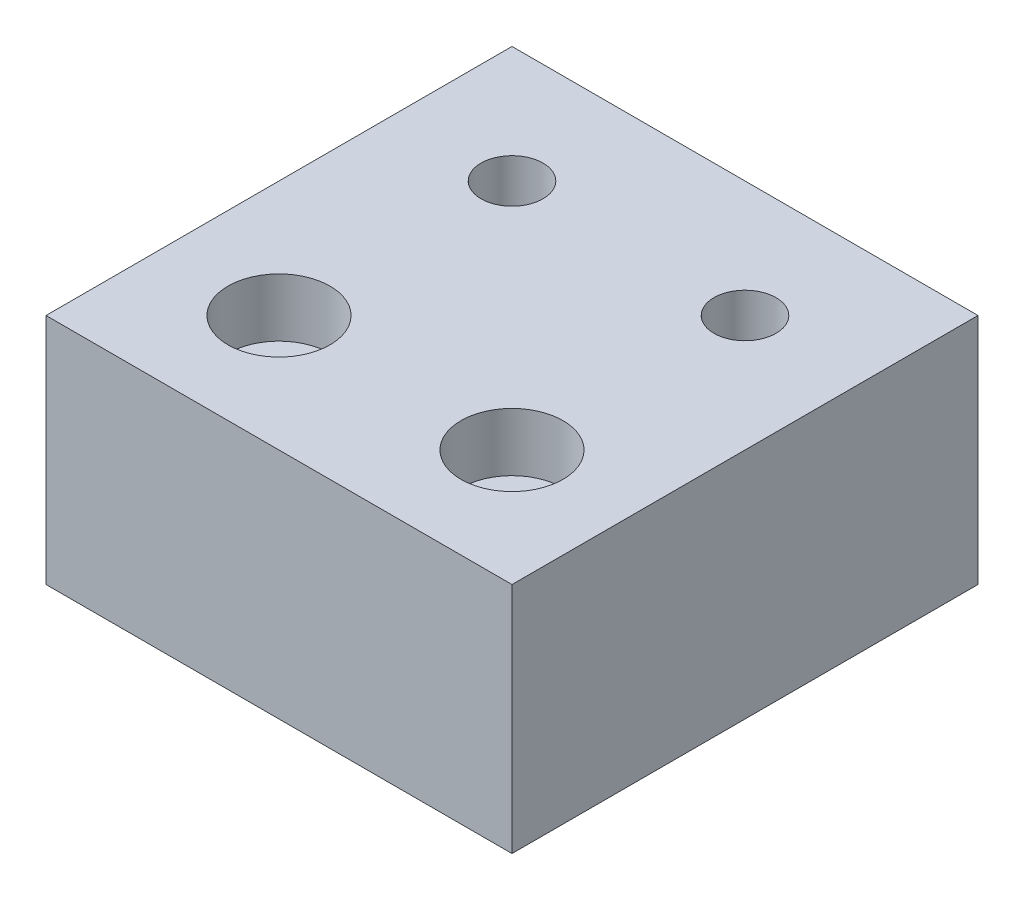
SolidWorks part; units mm, degrees
ref_plane "Front Plane" through (0, 0, 0) normal (0, 0, 1) x (1, 0, 0)
ref_plane "Top Plane" through (0, 0, 0) normal (0, 1, 0) x (1, 0, 0)
ref_plane "Right Plane" through (0, 0, 0) normal (1, 0, 0) x (0, 0, -1)
sketch "Sketch1" plane through (0, 0, 0) normal (0, 1, 0) x (1, 0, 0)
  line L1 (0, 0) -> (101.6, 0)
  line L2 (0, 0) -> (0, 50.8)
  line L3 (0, 50.8) -> (101.6, 50.8)
  line L4 (101.6, 0) -> (101.6, 50.8)
extrude "Boss-Extrude1" add sketch "Sketch1" along normal blind 25.4
hole_wizard "CBORE for 1/4 Socket Head Cap Screw1" positions "Sketch4" profile "Sketch3" counterbore size "1/4" standard "Ansi Inch" end condition through all
sketch "Sketch4" plane through (0, 25.4, 0) normal (0, 1, 0) x (-1, 0, 0)
  point P0 (-12.7, -12.7)
sketch "Sketch3" plane through (12.7, 25.4, -12.7) normal (1, 0, 0) x (0, 0, 1)
  line L0 (0, 0) -> (0, 25.4)
  line L1 (0, 25.4) -> (3.3782, 25.4)
  line L3 (3.3782, 25.4) -> (3.3782, 6.35)
  line L4 (3.3782, 6.35) -> (5.5562, 6.35)
  line L5 (5.5562, 6.35) -> (5.5563, 0)
  line L7 (5.5563, 0) -> (0, 0)
  line L11 (0, -6.35) -> (0, 107.95) construction
  dimension "Thru Hole Dia." = 6.7564
  dimension "Thru Hole Depth" = 25.4
  dimension "C'Bore Dia." = 11.1125
  dimension "C'Bore Depth" = 6.35
pattern_linear "LPattern1" count 1 spacing 25.4 along (0, 0, 1) count 4 spacing 25.4 along (1, 0, 0) of "CBORE for 1/4 Socket Head Cap Screw1"
hole_wizard "1/4 Clearance Hole1" positions "Sketch6" profile "Sketch5" hole size "1/4" standard "Ansi Inch" end condition through all
sketch "Sketch6" plane through (0, 25.4, 0) normal (0, 1, 0) x (-1, 0, 0)
  point P0 (-12.7, -38.1)
sketch "Sketch5" plane through (12.7, 25.4, -38.1) normal (1, 0, 0) x (0, 0, 1)
  line L0 (0, 0) -> (0, 25.4)
  line L1 (0, 25.4) -> (3.3782, 25.4)
  line L2 (3.3782, 25.4) -> (3.3782, 0)
  line L5 (3.3782, 0) -> (0, 0)
  line L11 (0, -6.35) -> (0, 107.95) construction
  dimension "Thru Hole Dia." = 6.7564
  dimension "Thru Hole Depth" = 25.4
pattern_linear "LPattern2" count 4 spacing 25.4 along (1, 0, 0) of "1/4 Clearance Hole1"
sketch "Sketch7" plane through (101.6, 0, 0) normal (1, 0, 0) x (0, 0, -1)
  line L1 (0, 0) -> (50.8, 0)
  line L2 (0, 0) -> (0, 25.4)
  line L3 (0, 25.4) -> (50.8, 25.4)
  line L4 (50.8, 0) -> (50.8, 25.4)
extrude "Cut-Extrude1" cut sketch "Sketch7" against normal blind 50.8
